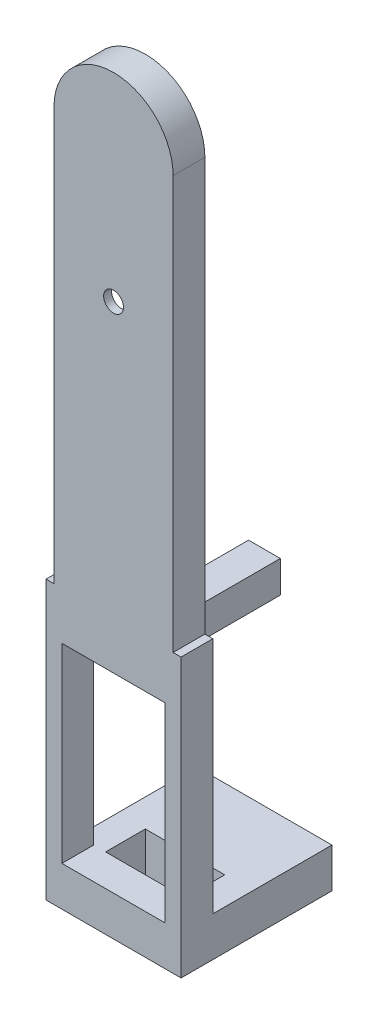
SolidWorks part; units mm, degrees
ref_plane "前基準面" through (0, 0, 0) normal (0, 0, 1) x (1, 0, 0)
ref_plane "上基準面" through (0, 0, 0) normal (0, 1, 0) x (1, 0, 0)
ref_plane "右基準面" through (0, 0, 0) normal (1, 0, 0) x (0, 0, -1)
sketch "草圖1" plane through (0, 0, 0) normal (0, 0, 1) x (1, 0, 0)
  line L0 (0, 0) -> (0, 4.6483) construction
  line L1 (7.5, 0) -> (7.5, 52)
  line L2 (7.5, 0) -> (-7.5, 0)
  line L3 (-7.5, 0) -> (-7.5, 52)
  arc A0 (7.5, 52) -> (-7.5, 52) centre (0, 52) ccw
  dimension "D1" = 7.5
  dimension "D2" = 52
extrude "填料-伸長1" add sketch "草圖1" along normal blind 4
sketch "草圖3" plane through (0, 0, 0) normal (0, 0, 1) x (1, 0, 0)
  line L0 (0, 0) -> (0, 14.8578) construction
  line L1 (7.5, 52) -> (-7.5, 52) construction
  line L2 (7.5, 15) -> (-7.5, 15) construction
  line L3 (7.5, 0) -> (7.5, 52) construction
  line L4 (-7.5, 52) -> (-7.5, 0) construction
  line L6 (7.5, 34.5) -> (5, 34.5) construction
  line L7 (5, 34.5) -> (2.1147, 16.658)
  line L8 (5, 34.5) -> (2.1328, 52)
  line L9 (-2.1328, 52) -> (-5, 34.5)
  line L10 (-5, 34.5) -> (-2.1422, 17)
  line L11 (0, 54.1328) -> (0, 59.5) construction
  line L12 (-5, 34.5) -> (-7.5, 34.5) construction
  arc A0 (7.5, 52) -> (-7.5, 52) centre (0, 52) ccw construction
  arc A1 (-4.7386, 36.0956) -> (-4.7403, 32.9094) centre (0, 34.5) ccw
  arc A2 (-2.1422, 17) -> (2.1147, 16.658) centre (0, 17) ccw
  arc A3 (-2.1328, 52) -> (2.1328, 52) centre (0, 52) cw
  arc A4 (4.7452, 32.9241) -> (4.7386, 36.0956) centre (0, 34.5) ccw
  dimension "D4" = 10
  dimension "D1" = 35
extrude "除料-伸長1" cut sketch "草圖3" along normal blind 3 contours A3 L9 L10 A2 L7 L8
sketch "草圖5" plane through (0, 0, 0) normal (0, 0, 1) x (1, 0, 0)
  line L0 (5, 34.5) -> (-5, 34.5) construction
  circle A0 centre (0, 34.5) radius 1.25
  dimension "D1" = 2.5
extrude "除料-伸長2" cut sketch "草圖5" along normal blind 12.4
sketch "草圖6" plane through (0, 0, 0) normal (0, 0, 1) x (1, 0, 0)
  line L0 (0, 62.3953) -> (0, -4.428) construction
  line L1 (0, -2.2) -> (0, 2.2) construction
  line L3 (8.5, 0) -> (-8.5, 0)
  line L4 (8.5, 0) -> (8.5, -35)
  line L5 (8.5, -35) -> (-8.5, -35)
  line L6 (-8.5, 0) -> (-8.5, -35)
  dimension "D1" = 17
  dimension "D2" = 8.5
  dimension "D3" = 35
extrude "填料-伸長2" add sketch "草圖6" along normal blind 4
sketch "草圖7" plane through (0, 0, 0) normal (0, 0, 1) x (1, 0, 0)
  line L0 (0, 64.1958) -> (0, -38.5274) construction
  line L1 (0, -2.2) -> (0, 2.2) construction
  line L3 (-6.5, -6) -> (6.5, -6)
  line L4 (-6.5, -6) -> (-6.5, -30)
  line L5 (-6.5, -30) -> (6.5, -30)
  line L6 (6.5, -6) -> (6.5, -30)
  line L7 (-8.5, -35) -> (8.5, -35) construction
  dimension "D1" = 6.5
  dimension "D2" = 13
  dimension "D3" = 24
  dimension "D4" = 5
extrude "除料-伸長3" cut sketch "草圖7" along normal blind 12.1
sketch "草圖8" plane through (0, 0, 0) normal (0, 0, 1) x (1, 0, 0)
  line L0 (0, 64.1958) -> (0, -34.8274) construction
  line L1 (0, -2.2) -> (0, 2.2) construction
  line L2 (0, 64.1958) -> (0, -39.0142) construction
  line L3 (6.5, -18) -> (-6.5, -18) construction
  line L4 (6.5, -30) -> (6.5, -6) construction
  line L5 (-6.5, -6) -> (-6.5, -30) construction
  line L6 (6.5, -6) -> (-6.5, -6) construction
  line L7 (2, -2) -> (-2, -2)
  line L8 (2, -2) -> (2, -6)
  line L9 (2, -6) -> (-2, -6)
  line L10 (-2, -2) -> (-2, -6)
  circle A0 centre (0, -4) radius 1.175
  dimension "D5" = 2.35
  dimension "D1" = 4
  dimension "D2" = 4
  dimension "D3" = 2
  dimension "D4" = 2
extrude "填料-伸長3" add sketch "草圖8" against normal blind 15
ref_plane "平面1" through (0, -35, 0) normal (0, 1, 0) x (1, 0, 0)
sketch "草圖9" plane through (0, -35, 0) normal (0, 1, 0) x (1, 0, 0)
  line L0 (0, 15.9246) -> (0, -4.8463) construction
  line L1 (0, -2.2) -> (0, 2.2) construction
  line L2 (-5, 0) -> (-5, 5)
  line L3 (7.5, 0) -> (-7.5, 0) construction
  line L4 (-5, 5) -> (5, 5)
  line L5 (-5, 0) -> (5, 0)
  line L6 (5, 0) -> (5, 5)
  line L12 (-8.5, 0) -> (8.5, 0)
  line L16 (8.5, 0) -> (8.5, 15)
  line L17 (8.5, 15) -> (-8.5, 15)
  line L19 (-8.5, 15) -> (-8.5, 0)
  point P12 (0, 0)
  point P13 (0, 5)
  point P20 (0, 0)
  point P21 (0, 15)
  point P25 (0, 0)
  point P26 (0, 15)
  dimension "D1" = 5
  dimension "D2" = 5
  dimension "D3" = 5
extrude "填料-伸長4" add sketch "草圖9" along normal blind 5
sketch "草圖10" plane through (0, 0, -15) normal (0, 0, -1) x (-1, 0, 0)
  line L0 (0, 0) -> (0, -35) construction
  line L1 (8.5, -35) -> (-8.5, -35) construction
  line L5 (8.538, -32.5) -> (-8.538, -32.5) construction
  circle A0 centre (0, -32.5) radius 1.175
  dimension "D2" = 2.35
  dimension "D1" = 2.5
extrude "除料-伸長4" cut sketch "草圖10" against normal blind 12.7 contours A0
